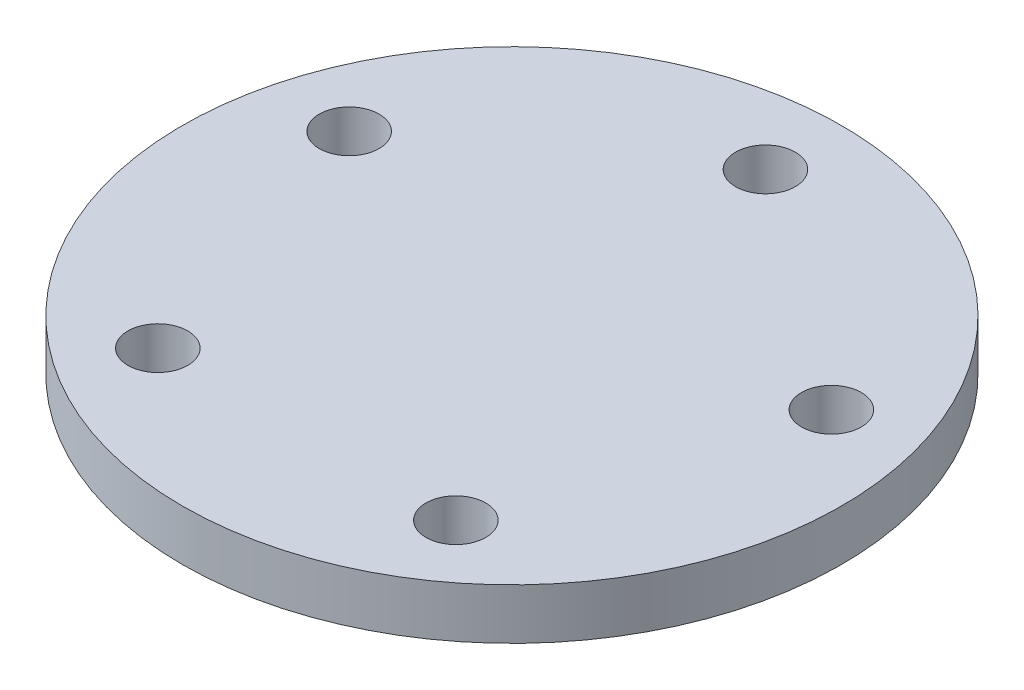
SolidWorks part; units mm, degrees
ref_plane "Front Plane" through (0, 0, 0) normal (0, 0, 1) x (1, 0, 0)
ref_plane "Top Plane" through (0, 0, 0) normal (0, 1, 0) x (1, 0, 0)
ref_plane "Right Plane" through (0, 0, 0) normal (1, 0, 0) x (0, 0, -1)
sketch "Sketch1" plane through (0, 0, 0) normal (0, 1, 0) x (1, 0, 0)
  circle A0 centre (0, 0) radius 17.5
  dimension "D1" = 35
extrude "Boss-Extrude1" add sketch "Sketch1" along normal blind 10
sketch "Sketch2" plane through (0, 10, 0) normal (0, 1, 0) x (1, 0, 0)
  circle A0 centre (0, 0) radius 32.5
  dimension "D1" = 65
extrude "Boss-Extrude2" add sketch "Sketch2" along normal blind 5
sketch "Sketch3" plane through (0, 15, 0) normal (0, 1, 0) x (1, 0, 0)
  circle A0 centre (0, 0) radius 25 construction
  circle A1 centre (0, 25) radius 2.95
  circle A2 centre (23.7764, 7.7254) radius 2.95
  circle A3 centre (14.6946, -20.2254) radius 2.95
  circle A4 centre (-14.6946, -20.2254) radius 2.95
  circle A5 centre (-23.7764, 7.7254) radius 2.95
  point P16 (0, 0)
  dimension "D1" = 5.9
  dimension "D2" = 5
extrude "Cut-Extrude1" cut sketch "Sketch3" against normal blind 7
